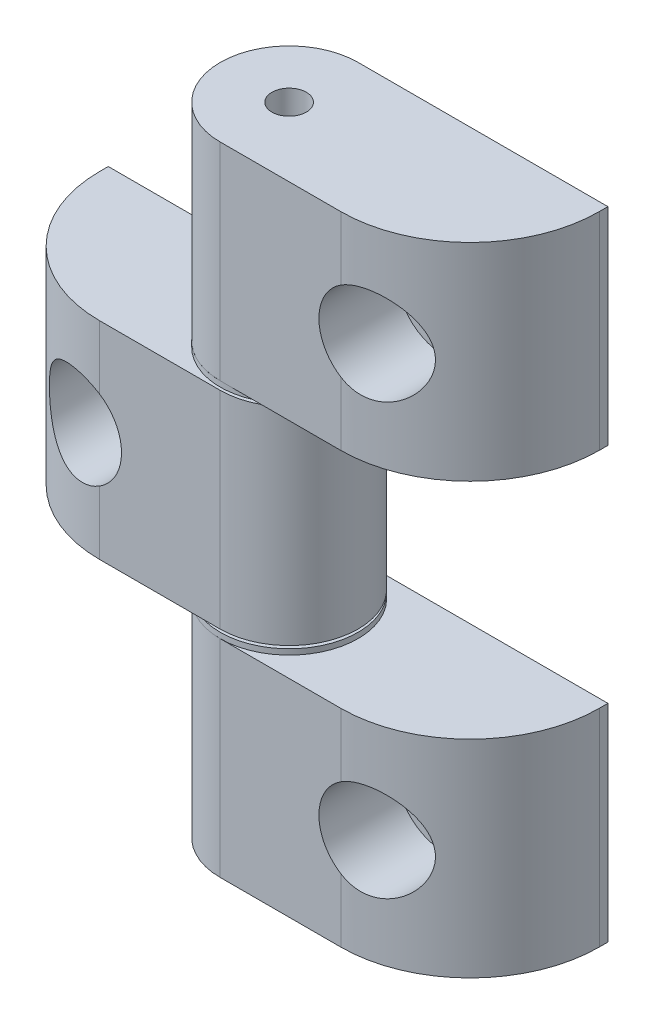
SolidWorks part; units mm, degrees
ref_plane "Front Plane" through (0, 0, 0) normal (0, 0, 1) x (1, 0, 0)
ref_plane "Top Plane" through (0, 0, 0) normal (0, 1, 0) x (1, 0, 0)
ref_plane "Right Plane" through (0, 0, 0) normal (1, 0, 0) x (0, 0, -1)
sketch "Sketch1" plane through (0, 0, 0) normal (0, 0, 1) x (1, 0, 0)
  line L0 (0, 26.5933) -> (0, -25.9627) construction
  line L1 (0, 0) -> (19.7866, 0) construction
  line L2 (-9.5758, 9.525) -> (19.7866, 9.525)
  line L3 (-9.5758, 9.525) -> (-9.5758, -9.525)
  line L4 (-9.5758, -9.525) -> (19.7866, -9.525)
  line L5 (19.7866, 9.525) -> (19.7866, -9.525)
  circle A0 centre (0, 0) radius 2.413
  dimension "K" = 4.826
  dimension "C" = 19.05
  dimension "G" = 9.5758
  dimension "A" = 29.3624
extrude "Extrude1" add sketch "Sketch1" along normal mid plane 12.7
sketch "Sketch2" plane through (0, 0, -6.35) normal (0, 0, -1) x (-1, 0, 0)
  circle A1 centre (0, 0) radius 2.413 construction
  circle A2 centre (0, 0) radius 4.191
  circle A3 centre (0, 0) radius 4.191
  circle A4 centre (0, 0) radius 2.413
  dimension "D1" = 1.778
extrude "Extrude2" add sketch "Sketch2" along normal blind 2.159
sketch "Sketch3" plane through (0, -9.525, 0) normal (0, -1, 0) x (1, 0, 0)
  line L0 (-9.5758, 6.35) -> (19.7866, 6.35) construction
  line L1 (19.7866, 6.35) -> (19.7866, -6.35) construction
  line L2 (-9.5758, -6.35) -> (19.7866, -6.35) construction
  line L3 (-9.5758, 6.35) -> (-9.5758, -6.35) construction
  line L4 (-9.5758, 6.35) -> (2.3305, 6.35)
  line L5 (-9.5758, 6.35) -> (-9.5758, -5.5562)
  line L6 (13.4366, 6.35) -> (13.4366, 7.62)
  line L7 (13.4366, 7.62) -> (21.0566, 7.62)
  line L8 (21.0566, 7.62) -> (21.0566, -7.62)
  line L9 (13.4366, -6.35) -> (13.4366, -7.62)
  line L10 (13.4366, -7.62) -> (21.0566, -7.62)
  line L11 (19.7866, 0) -> (21.0566, 0) construction
  circle A0 centre (13.4366, 0) radius 1.5875
  arc A1 (13.4366, -6.35) -> (13.4366, 6.35) centre (13.4366, 0) ccw
  arc A2 (-9.5758, -5.5562) -> (2.3305, 6.35) centre (2.3305, -5.5562) cw
  dimension "D2" = 3.175
  dimension "D1" = 1.27
  dimension "D3" = 0.7937
extrude "Cut-Extrude1" cut sketch "Sketch3" against normal through all
sketch "Sketch4" plane through (0, 0, 6.35) normal (0, 0, 1) x (1, 0, 0)
  circle A0 centre (0, 0) radius 4.3434
  dimension "D1" = 8.6868
extrude "Cut-Extrude2" cut sketch "Sketch4" against normal blind 7.1501
ref_plane "Plane1" through (13.4366, 0, 0) normal (1, 0, 0) x (0, 0, -1)
mirror "Mirror1" about plane through (13.4366, 0, 0) normal (1, 0, 0) of bodies 104
pattern_linear "LPattern1" count 2 spacing 19.812 along (0, -1, 0) count 2 spacing 19.812 along (0, 1, 0) of bodies 105
delete or keep bodies "Body-Delete1" type delete bodies bodies 105
delete or keep bodies "Body-Delete2" type delete bodies bodies 108
sketch "Sketch5" plane through (0, -10.287, 0) normal (0, 1, 0) x (1, 0, 0)
  circle A0 centre (13.4366, 0) radius 6.35
  circle A1 centre (13.4366, 0) radius 1.5875 construction
  circle A2 centre (13.4366, 0) radius 1.5875
  arc A3 (13.4366, 6.35) -> (13.4366, -6.35) centre (13.4366, 0) ccw construction
extrude "Extrude3" add sketch "Sketch5" along normal blind 0.508 separate body
sketch "Sketch6" plane through (0, 10.287, 0) normal (0, -1, 0) x (1, 0, 0)
  circle A0 centre (13.4366, 0) radius 6.35
  circle A1 centre (13.4366, 0) radius 1.5875 construction
  circle A2 centre (13.4366, 0) radius 1.5875
  arc A3 (13.4366, 6.35) -> (13.4366, -6.35) centre (13.4366, 0) ccw construction
extrude "Extrude4" add sketch "Sketch6" along normal blind 0.508 separate body
sketch "Sketch7" plane through (0, 0, 0) normal (0, 1, 0) x (1, 0, 0)
  circle A0 centre (13.4366, 0) radius 1.5875 construction
  circle A1 centre (13.4366, 0) radius 1.5875
extrude "Extrude5" add sketch "Sketch7" against normal offset from surface 9.144 and the other way offset from surface (19.431 mm away) 9.144 up to face at (13.4366, -10.287, 6.35) offset beyond the face yes other way up to face at (13.4366, 10.287, -6.35)
chamfer "Chamfer1" distance 0.508 angle 45 2 edges at (13.4366, -19.431, 1.5875) (13.4366, 19.431, -1.5875)
sketch "Sketch8" plane through (0, 9.525, 0) normal (0, 1, 0) x (1, 0, 0)
  line L3 (2.3305, -6.35) -> (13.4366, -6.35)
  line L4 (13.4366, 6.35) -> (-9.5758, 6.35)
  line L5 (-9.5758, 6.35) -> (-9.5758, 5.5563)
  line L6 (2.3305, -6.35) -> (13.4366, -6.35)
  line L7 (13.4366, 6.35) -> (-9.5758, 6.35)
  line L8 (-9.5758, 6.35) -> (-9.5758, 5.5563)
  arc A2 (13.4366, -6.35) -> (13.4366, 6.35) centre (13.4366, 0) ccw
  arc A3 (-9.5758, 5.5563) -> (2.3305, -6.35) centre (2.3305, 5.5562) ccw
  arc A4 (13.4366, -6.35) -> (13.4366, 6.35) centre (13.4366, 0) ccw
  arc A5 (-9.5758, 5.5563) -> (2.3305, -6.35) centre (2.3305, 5.5562) ccw
  dimension "D1" = 0
extrude "Cut-Extrude3" [suppressed] cut sketch "Sketch8" against normal up to surface (19.05 mm away)
equation "\"D1@Sketch4\" = \"K@Sketch1\"*1.8"
